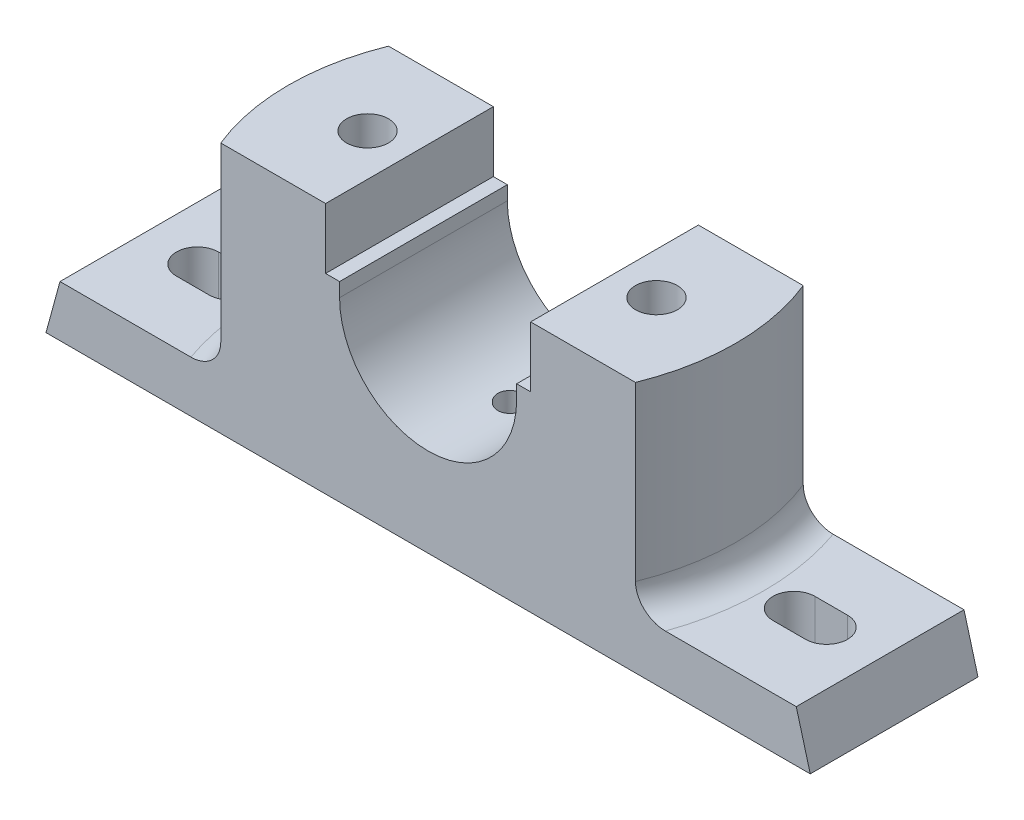
SolidWorks part; units mm, degrees
ref_plane "Front Plane" through (0, 0, 0) normal (0, 0, 1) x (1, 0, 0)
ref_plane "Top Plane" through (0, 0, 0) normal (0, 1, 0) x (1, 0, 0)
ref_plane "Right Plane" through (0, 0, 0) normal (1, 0, 0) x (0, 0, -1)
sketch "Sketch1" plane through (0, 0, 0) normal (0, 0, 1) x (1, 0, 0)
  line L0 (-82, 0) -> (82, 0)
  line L1 (82, 0) -> (79, 11)
  line L2 (79, 11) -> (50, 11)
  line L3 (50, 11) -> (50, 54)
  line L4 (50, 54) -> (22, 54)
  line L5 (22, 54) -> (22, 41)
  line L6 (22, 41) -> (19, 41)
  line L7 (0, 0) -> (0, 105.7946) construction
  line L8 (-22, 41) -> (-19, 41)
  line L9 (-22, 54) -> (-22, 41)
  line L10 (-50, 54) -> (-22, 54)
  line L11 (-50, 11) -> (-50, 54)
  line L12 (-79, 11) -> (-50, 11)
  line L13 (-82, 0) -> (-79, 11)
  line L14 (-19, 38) -> (-19, 41)
  line L15 (19, 38) -> (19, 41)
  arc A0 (19, 38) -> (0, 19) centre (0, 38) cw
  arc A1 (-19, 38) -> (0, 19) centre (0, 38) ccw
  dimension "D5" = 19
  dimension "D9" = 50
  dimension "D10" = 16
  dimension "D1" = 164
  dimension "D2" = 11
  dimension "D3" = 3
  dimension "D4" = 54
  dimension "D7" = 44
  dimension "D8" = 13
extrude "Boss-Extrude1" add sketch "Sketch1" along normal mid plane 36
sketch "Sketch5" plane through (0, 54, 0) normal (0, 1, 0) x (1, 0, 0)
  line L0 (-22, 18) -> (-50, 18) construction
  line L1 (-22, -18) -> (-50, -18) construction
  line L2 (-50, -18) -> (-50, 18) construction
  line L3 (50, -18) -> (22, -18) construction
  line L4 (50, 18) -> (22, 18) construction
  line L5 (50, -18) -> (50, 18) construction
  line L6 (-44.4972, 18) -> (-50, 18)
  line L7 (-44.4972, -18) -> (-50, -18)
  line L8 (-50, -18) -> (-50, 18)
  line L9 (50, -18) -> (44.4972, -18)
  line L10 (50, 18) -> (44.4972, 18)
  line L11 (50, -18) -> (50, 18)
  arc A0 (-44.4972, 18) -> (-44.4972, -18) centre (0, 0) ccw
  arc A1 (44.4972, -18) -> (44.4972, 18) centre (0, 0) ccw
  dimension "D1" = 48
extrude "Cut-Extrude1" cut sketch "Sketch5" against normal up to surface (43 mm away) up to face at (-64.5, 11, 0)
fillet "Fillet2" radius 6 2 edges at (48, 11, 0) (-48, 11, 0)
hole_wizard "Ø6.0 (6) Diameter Hole1" positions "3DSketch3" profile "Sketch19" hole size "Ø6.0" standard "ANSI Metric"
sketch3d "3DSketch3"
  point P0 (0, 19, 0)
  dimension "D1" = 0
  dimension "D2" = 0
sketch "Sketch19" plane through (0, 19, 0) normal (1, 0, 0) x (0, 0, 1)
  line L0 (0, 0) -> (0, 7.8026)
  line L1 (0, 7.8026) -> (3, 6)
  line L2 (3, 6) -> (3, 0)
  line L5 (3, 0) -> (0, 0)
  line L10 (0, 7.8026) -> (-3, 6) construction
  line L11 (0, -6.35) -> (0, 107.95) construction
  dimension "Hole Dia." = 6
  dimension "Hole Depth" = 6
  dimension "Drill Angle" = 118
sketch "Sketch20" plane through (0, 11, 0) normal (0, 1, 0) x (1, 0, 0)
  line L0 (-67.5, 0) -> (-60.5, 0) construction
  line L1 (-67.5, 4.5) -> (-60.5, 4.5)
  line L2 (-67.5, -4.5) -> (-60.5, -4.5)
  arc A0 (-67.5, 4.5) -> (-67.5, -4.5) centre (-67.5, 0) ccw
  arc A1 (-60.5, -4.5) -> (-60.5, 4.5) centre (-60.5, 0) ccw
  point P2 (-64, 0)
  dimension "D1" = 16
  dimension "D2" = 9
  dimension "D3" = 64
extrude "Cut-Extrude2" cut sketch "Sketch20" against normal through all
hole_wizard "Ø6.0 (6) Diameter Hole2" positions "Sketch22" profile "Sketch23" hole size "Ø6.0" standard "ANSI Metric" end condition through all
sketch "Sketch22" plane through (0, 54, 0) normal (0, 1, 0) x (1, 0, 0)
  point P0 (-31, 0)
  dimension "D1" = 31
sketch "Sketch23" plane through (-31, 54, 0) normal (1, 0, 0) x (0, 0, 1)
  line L0 (0, 0) -> (0, 54)
  line L1 (0, 54) -> (4.5, 54)
  line L2 (4.5, 54) -> (4.5, 0)
  line L5 (4.5, 0) -> (0, 0)
  line L11 (0, -6.35) -> (0, 107.95) construction
  dimension "Thru Hole Dia." = 9
  dimension "Thru Hole Depth" = 54
sketch "Sketch24" plane through (0, 0, 0) normal (0, -1, 0) x (1, 0, 0)
  line L1 (-41, 10) -> (-21, 10)
  line L2 (-41, 10) -> (-41, -10)
  line L3 (-41, -10) -> (-21, -10)
  line L4 (-21, 10) -> (-21, -10)
  line L5 (-41, 10) -> (-21, -10) construction
  line L6 (-41, -10) -> (-21, 10) construction
  point P0 (-31, 0)
  dimension "D1" = 20
  dimension "D2" = 20
extrude "Cut-Extrude3" cut sketch "Sketch24" against normal blind 8
mirror "Mirror1" about plane through (0, 0, 0) normal (1, 0, 0) of "Cut-Extrude3", "Cut-Extrude2", "Ø6.0 (6) Diameter Hole2"
